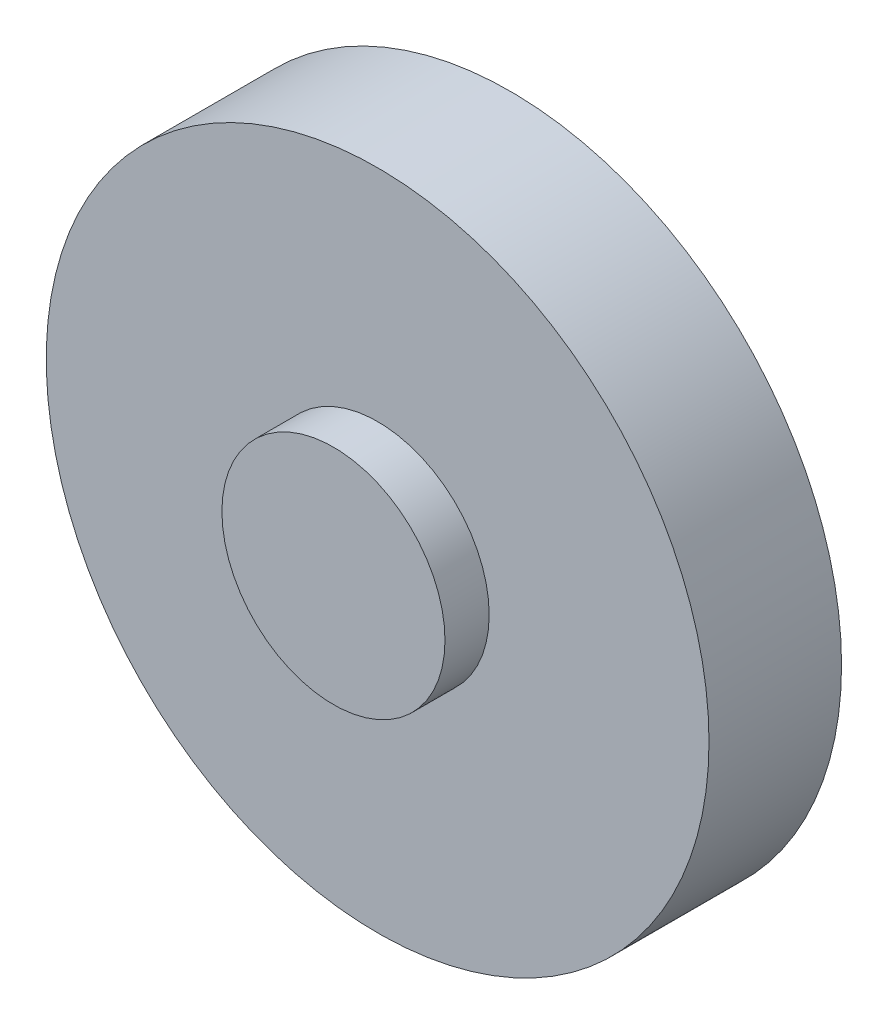
SolidWorks part; units mm, degrees
ref_plane "Front Plane" through (0, 0, 0) normal (0, 0, 1) x (1, 0, 0)
ref_plane "Top Plane" through (0, 0, 0) normal (0, 1, 0) x (1, 0, 0)
ref_plane "Right Plane" through (0, 0, 0) normal (1, 0, 0) x (0, 0, -1)
sketch "Sketch1" plane through (0, 0, 0) normal (0, 0, 1) x (1, 0, 0)
  circle A0 centre (0, 0) radius 150
  dimension "D1" = 300
extrude "Boss-Extrude1" add sketch "Sketch1" along normal blind 60
sketch "Sketch2" plane through (0, 0, 60) normal (0, 0, 1) x (1, 0, 0)
  circle A0 centre (0, 0) radius 50.4923
extrude "Boss-Extrude2" add sketch "Sketch2" along normal blind 20
sketch "Sketch3" plane through (0, 0, 0) normal (0, 0, -1) x (-1, 0, 0)
  circle A0 centre (0, 0) radius 49.3461
extrude "Boss-Extrude3" add sketch "Sketch3" along normal blind 20
